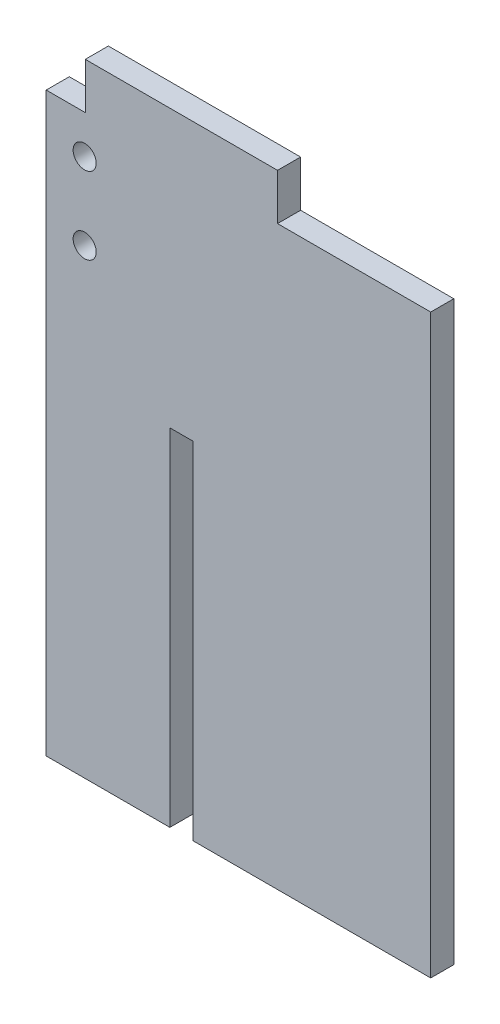
SolidWorks part; units mm, degrees
ref_plane "Front Plane" through (0, 0, 0) normal (0, 0, 1) x (1, 0, 0)
ref_plane "Top Plane" through (0, 0, 0) normal (0, 1, 0) x (1, 0, 0)
ref_plane "Right Plane" through (0, 0, 0) normal (1, 0, 0) x (0, 0, -1)
sketch "Sketch1" plane through (0, 0, 0) normal (0, 0, 1) x (1, 0, 0)
  line L0 (12.5, 73.8577) -> (-12.5, 73.8577)
  line L1 (-12.5, 73.8577) -> (-12.5, 67.8577)
  line L2 (-12.5, 67.8577) -> (-17.58, 67.8577)
  line L3 (-17.58, 67.8577) -> (-17.58, -7.1423)
  line L4 (-17.58, -7.1423) -> (-1.5, -7.1423)
  line L5 (-1.5, -7.1423) -> (-1.5, 37.8577)
  line L6 (-1.5, 37.8577) -> (1.5, 37.8577)
  line L7 (1.5, 37.8577) -> (1.5, -7.1423)
  line L8 (1.5, -7.1423) -> (32.42, -7.1423)
  line L9 (32.42, -7.1423) -> (32.42, 67.8577)
  line L10 (32.42, 67.8577) -> (12.5, 67.8577)
  line L11 (12.5, 67.8577) -> (12.5, 73.8577)
  point P2 (0, 73.8577)
  dimension "D1" = 3
  dimension "D2" = 30
  dimension "D3" = 50
  dimension "D4" = 25
  dimension "D5" = 75
  dimension "D6" = 6
  dimension "D7" = 16.08
  dimension "D8" = 5.08
extrude "Boss-Extrude1" add sketch "Sketch1" along normal blind 3
sketch "Sketch2" plane through (0, 0, 3) normal (0, 0, 1) x (1, 0, 0)
  line L0 (-17.58, 67.8577) -> (-17.58, -7.1423) construction
  line L1 (-12.5, 67.8577) -> (-17.58, 67.8577) construction
  circle A0 centre (-12.58, 62.8577) radius 1.5
  circle A1 centre (-12.58, 52.8577) radius 1.5
  dimension "D1" = 3
  dimension "D2" = 10
  dimension "D3" = 5
  dimension "D4" = 5
extrude "Cut-Extrude1" cut sketch "Sketch2" against normal through all
